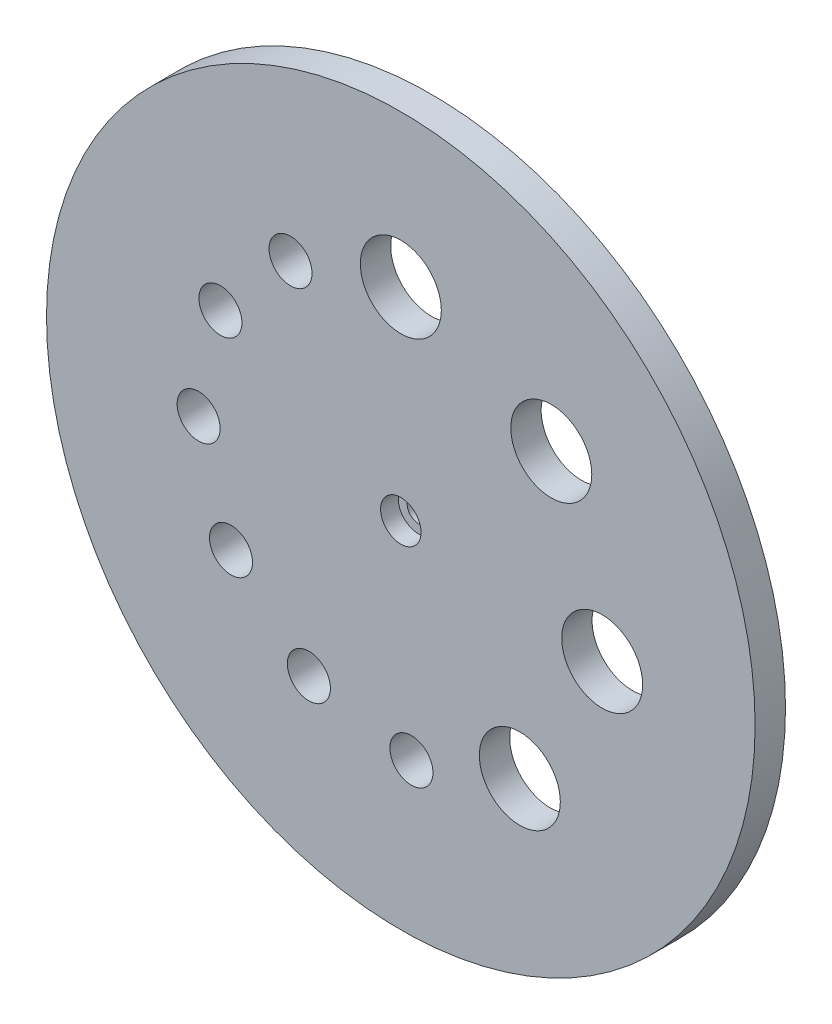
SolidWorks part; units mm, degrees
material "356.0-T6 Permanent Mold cast (SS)"
ref_plane "Front Plane" through (0, 0, 0) normal (0, 0, 1) x (1, 0, 0)
ref_plane "Top Plane" through (0, 0, 0) normal (0, 1, 0) x (1, 0, 0)
ref_plane "Right Plane" through (0, 0, 0) normal (1, 0, 0) x (0, 0, -1)
sketch "Sketch2" plane through (0, 0, 0) normal (0, 0, 1) x (1, 0, 0)
  circle A0 centre (0, 0) radius 140
  dimension "D1" = 280
extrude "Boss-Extrude1" add sketch "Sketch2" along normal blind 12
sketch "Sketch3" plane through (0, 0, 12) normal (0, 0, 1) x (1, 0, 0)
  circle A0 centre (59.4516, 53.5304) radius 16
  circle A1 centre (0, 80) radius 16
  circle A2 centre (79.5618, -8.3623) radius 16
  circle A3 centre (47.0228, -64.7214) radius 16
  circle A4 centre (-16.6329, -78.2518) radius 16 [skipped]
  circle A5 centre (4.1869, -79.8904) radius 8.5
  circle A6 centre (-36.3192, -71.2805) radius 8.5
  circle A7 centre (-67.0936, -43.5711) radius 8.5
  circle A8 centre (-79.8904, -4.1869) radius 8.5
  circle A9 centre (-71.2805, 36.3192) radius 8.5
  circle A10 centre (-43.5711, 67.0936) radius 8.5
  circle A12 centre (-4.1869, 79.8904) radius 8.5 [skipped]
  dimension "D1" = 80
  dimension "D3" = 32
  dimension "D4" = 80
  dimension "D7" = 33
  dimension "D8" = 17
  dimension "D9" = 33
  dimension "D5" = 48
  dimension "D2" = 4
  dimension "D6" = 6
extrude "Cut-Extrude1" cut sketch "Sketch3" against normal through all
hole_wizard "CBORE for M5 Hex Head Bolt1" positions "Sketch5" profile "Sketch6" counterbore size "M5" standard "Ansi Metric" end condition through all
sketch "Sketch5" plane through (0, 0, 12) normal (0, 0, 1) x (1, 0, 0)
  point P0 (0, 0)
  dimension "D1" = 0
sketch "Sketch6" plane through (0, 0, 12) normal (1, 0, 0) x (0, -1, 0)
  line L0 (0, 0) -> (0, 12)
  line L1 (0, 12) -> (4.5, 12)
  line L3 (4.5, 12) -> (4.5, 7)
  line L4 (4.5, 7) -> (8, 7)
  line L5 (8, 7) -> (8, 0)
  line L7 (8, 0) -> (0, 0)
  line L11 (0, -6.35) -> (0, 107.95) construction
  dimension "Thru Hole Dia." = 9
  dimension "Thru Hole Depth" = 12
  dimension "C'Bore Dia." = 16
  dimension "C'Bore Depth" = 7
